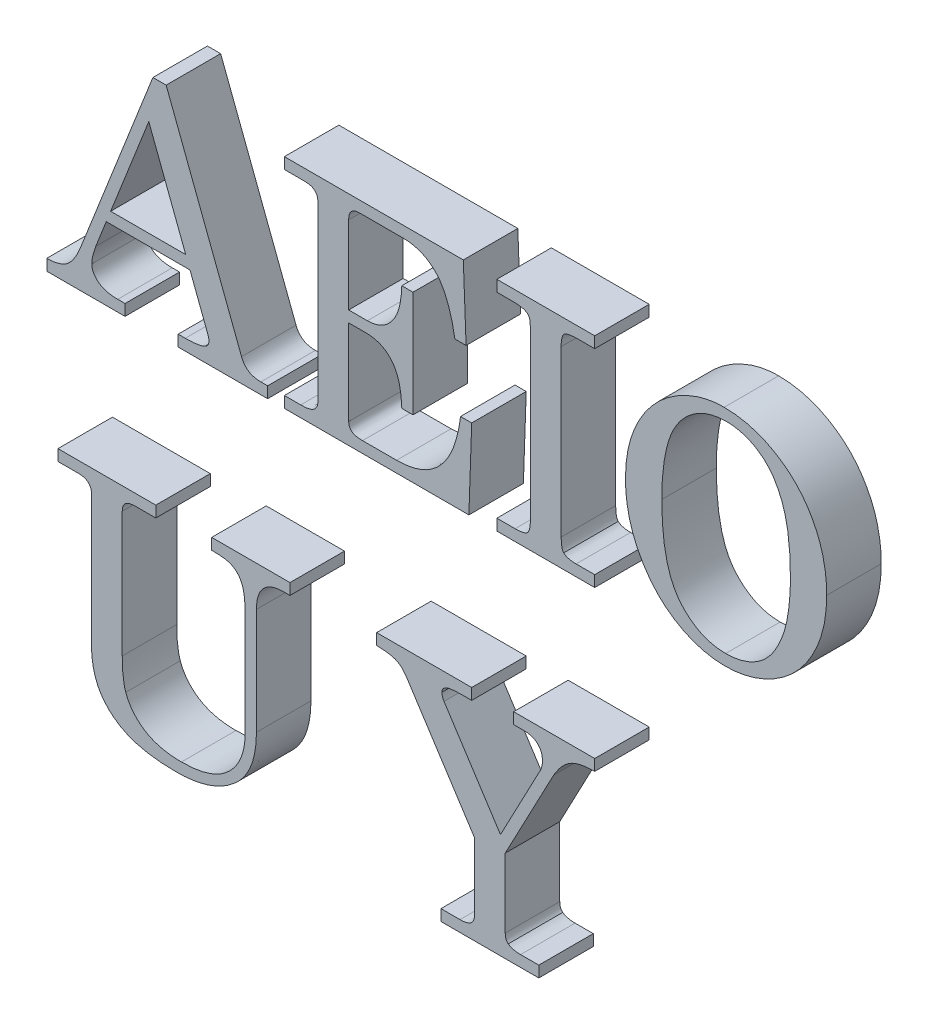
SolidWorks part; units mm, degrees
ref_plane "Plan de face" through (0, 0, 0) normal (0, 0, 1) x (1, 0, 0)
ref_plane "Plan de dessus" through (0, 0, 0) normal (0, 1, 0) x (1, 0, 0)
ref_plane "Plan de droite" through (0, 0, 0) normal (1, 0, 0) x (0, 0, -1)
sketch "Esquisse1" plane through (0, 0, 0) normal (0, 0, 1) x (1, 0, 0)
  text T0 "AEIO\r\nU Y" font "Century Schoolbook" height 40
  point P1 (0, 0)
extrude "Boss.-Extru.1" add sketch "Esquisse1" along normal blind 10
